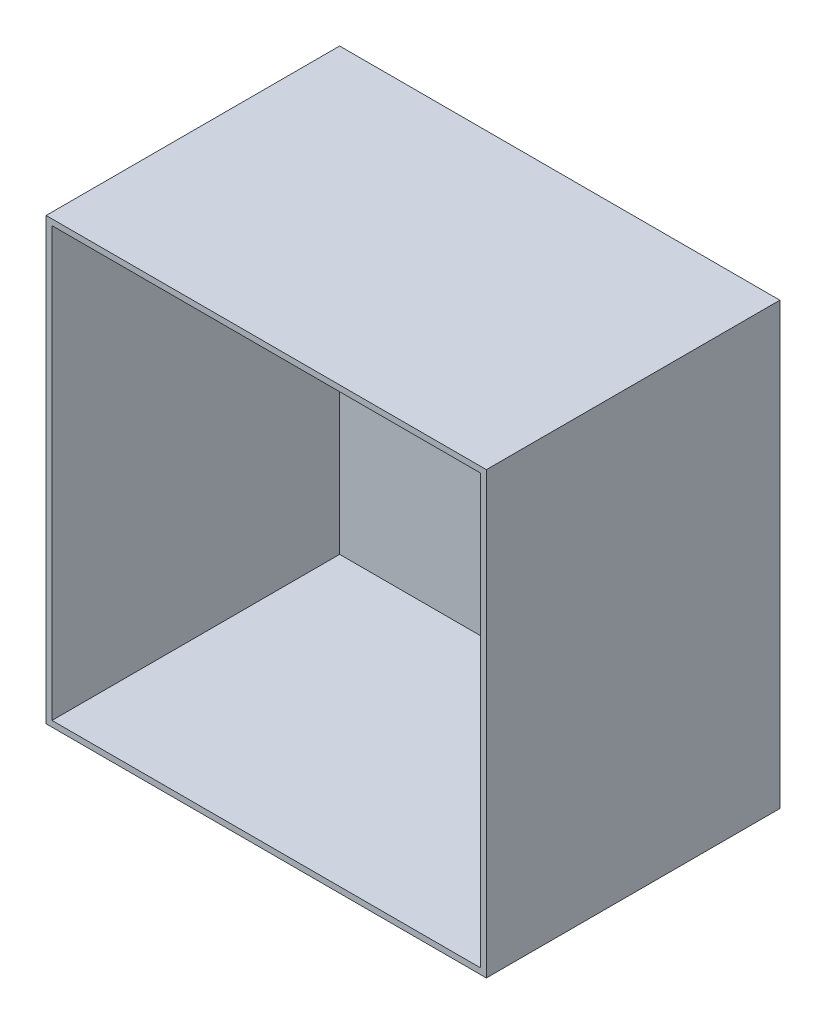
SolidWorks part; units mm, degrees
ref_plane "前视基准面" through (0, 0, 0) normal (0, 0, 1) x (1, 0, 0)
ref_plane "上视基准面" through (0, 0, 0) normal (0, 1, 0) x (1, 0, 0)
ref_plane "右视基准面" through (0, 0, 0) normal (1, 0, 0) x (0, 0, -1)
sketch "草图1" plane through (0, 0, 0) normal (0, 0, 1) x (1, 0, 0)
  line L1 (75, -75) -> (-75, -75)
  line L2 (75, -75) -> (75, 75)
  line L3 (75, 75) -> (-75, 75)
  line L4 (-75, -75) -> (-75, 75)
  line L5 (75, -75) -> (-75, 75) construction
  line L6 (75, 75) -> (-75, -75) construction
  point P0 (0, 0)
  dimension "D1" = 150
  dimension "D2" = 150
extrude "凸台-拉伸1" add sketch "草图1" along normal blind 100
shell "抽壳1" thickness 2
